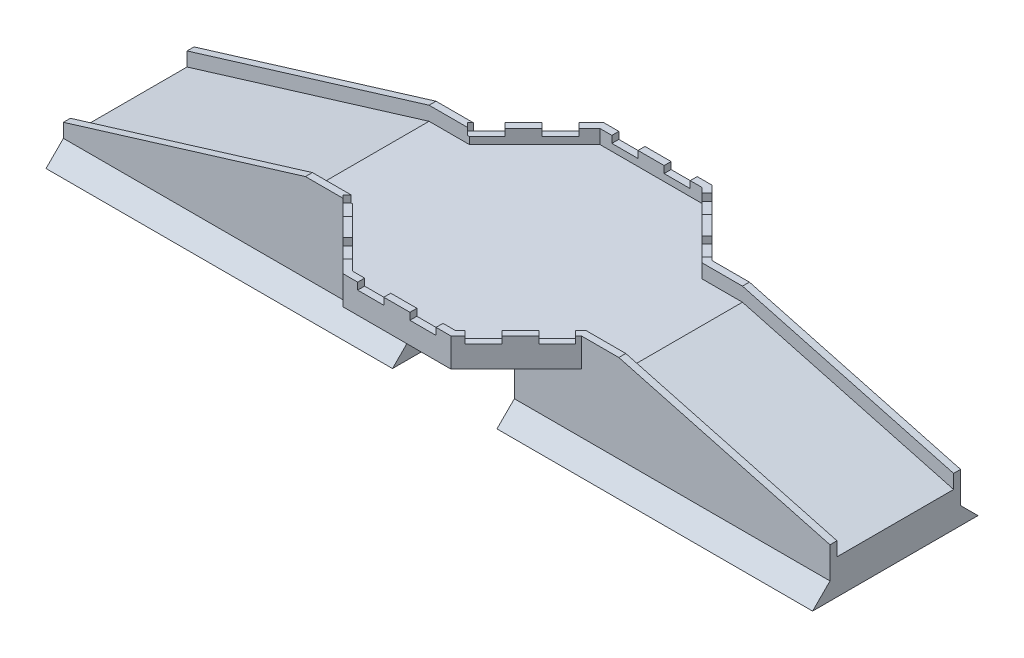
SolidWorks part; units mm, degrees
ref_plane "前视基准面" through (0, 0, 0) normal (0, 0, 1) x (1, 0, 0)
ref_plane "上视基准面" through (0, 0, 0) normal (0, 1, 0) x (1, 0, 0)
ref_plane "右视基准面" through (0, 0, 0) normal (1, 0, 0) x (0, 0, -1)
sketch "草图1" plane through (0, 0, 0) normal (0, 1, 0) x (1, 0, 0)
  line L1 (1371.3203, 750) -> (621.3203, 1500)
  line L2 (621.3203, 1500) -> (-621.3203, 1500)
  line L3 (-621.3203, 1500) -> (-1371.3203, 750)
  line L5 (-1371.3203, -750) -> (-621.3203, -1500)
  line L6 (-621.3203, -1500) -> (621.3203, -1500)
  line L7 (621.3203, -1500) -> (1371.3203, -750)
  line L9 (-1371.3203, 750) -> (-1800, 750)
  line L11 (1338.1833, 670) -> (588.1833, 1420)
  line L12 (588.1833, 1420) -> (-588.1833, 1420)
  line L13 (-588.1833, 1420) -> (-1338.1833, 670)
  line L15 (-1338.1833, -670) -> (-588.1833, -1420)
  line L16 (-588.1833, -1420) -> (588.1833, -1420)
  line L17 (588.1833, -1420) -> (1338.1833, -670)
  line L18 (-1800, 750) -> (-1800, 670)
  line L19 (-1800, 670) -> (-1338.1833, 670)
  line L20 (-1371.3203, -750) -> (-1800, -750)
  line L21 (-1800, -750) -> (-1800, -670)
  line L22 (-1800, -670) -> (-1338.1833, -670)
  line L23 (1371.3203, 750) -> (1800, 750)
  line L24 (1800, 750) -> (1800, 670)
  line L25 (1800, 670) -> (1338.1833, 670)
  line L26 (1371.3203, -750) -> (1800, -750)
  line L27 (1800, -750) -> (1800, -670)
  line L28 (1800, -670) -> (1338.1833, -670)
  line L31 (-1420, 586.3768) -> (-1420, 539.5139) [skipped]
  line L32 (-1500, 621.3203) -> (-1500, 541.3203) [skipped]
  line L33 (1420, -589.9897) -> (1420, -543.1268) [skipped]
  line L34 (1500, -621.3203) -> (1500, -541.3203) [skipped]
  dimension "D1" = 3000
  dimension "D2" = 80
  dimension "D3" = 80
  dimension "D4" = 2840
  dimension "D5" = 3600
  dimension "D6" = 3600
  dimension "D7" = 1500
  dimension "D8" = 750
  dimension "D9" = 80
  dimension "D10" = 80
  dimension "D11" = 80
  dimension "D12" = 80
  dimension "D13" = 1500
  dimension "D14" = 750
extrude "凸台-拉伸1" add sketch "草图1" along normal blind 80
sketch "草图2" plane through (0, 80, 0) normal (0, 1, 0) x (1, 0, 0)
  line L0 (588.1833, -1420) -> (-588.1833, -1420) construction
  line L1 (-150, -1420) -> (150, -1420)
  line L2 (-150, -1420) -> (-150, -1500)
  line L3 (-150, -1500) -> (150, -1500)
  line L4 (150, -1420) -> (150, -1500)
  line L5 (-621.3203, -1500) -> (621.3203, -1500) construction
  line L6 (450, -1420) -> (450, -1500)
  line L7 (450, -1500) -> (621.3203, -1500)
  line L8 (621.3203, -1500) -> (701.5537, -1419.7666)
  line L9 (621.3203, -1500) -> (1371.3203, -750) construction
  line L10 (701.5537, -1419.7666) -> (644.9852, -1363.1981)
  line L11 (1338.1833, -670) -> (588.1833, -1420) construction
  line L12 (644.9852, -1363.1981) -> (588.1833, -1420)
  line L13 (588.1833, -1420) -> (450, -1420)
  line L14 (1069.2493, -938.934) -> (857.1172, -1151.066)
  line L15 (1069.2493, -938.934) -> (1125.8178, -995.5025)
  line L16 (857.1172, -1151.066) -> (913.6858, -1207.6346)
  line L17 (1125.8178, -995.5025) -> (913.6858, -1207.6346)
  line L18 (1281.3813, -726.8019) -> (1338.1833, -670)
  line L19 (1338.1833, -670) -> (1800, -670)
  line L20 (1800, -670) -> (1800, -750)
  line L21 (1800, -750) -> (1371.3203, -750)
  line L22 (1371.3203, -750) -> (1337.9499, -783.3705)
  line L23 (1337.9499, -783.3705) -> (1281.3813, -726.8019)
  line L24 (0, 0) -> (348.169, 0)
  line L25 (-1403.7125, -717.6079) -> (-1347.1439, -661.0393)
  line L26 (-1371.3203, -750) -> (-1403.7125, -717.6079)
  line L27 (-1800, -750) -> (-1371.3203, -750)
  line L28 (-1800, -670) -> (-1800, -750)
  line L29 (-1338.1833, -670) -> (-1800, -670)
  line L30 (-1347.1439, -661.0393) -> (-1338.1833, -670)
  line L31 (-1189.2544, -932.0659) -> (-977.1224, -1144.198)
  line L32 (-920.5538, -1087.6294) -> (-977.1224, -1144.198)
  line L33 (-1132.6859, -875.4974) -> (-1189.2544, -932.0659)
  line L34 (-1132.6859, -875.4974) -> (-920.5538, -1087.6294)
  line L35 (-588.1833, -1420) -> (-450, -1420)
  line L36 (-708.4218, -1299.7615) -> (-588.1833, -1420)
  line L37 (-764.9903, -1356.33) -> (-708.4218, -1299.7615)
  line L38 (-621.3203, -1500) -> (-764.9903, -1356.33)
  line L39 (-450, -1500) -> (-621.3203, -1500)
  line L40 (-450, -1420) -> (-450, -1500)
  line L41 (-150, -1420) -> (-150, -1500)
  line L42 (150, -1420) -> (150, -1500)
  line L43 (150, 1420) -> (150, 1500)
  line L44 (-150, 1420) -> (-150, 1500)
  line L45 (-450, 1420) -> (-450, 1500)
  line L46 (-450, 1500) -> (-621.3203, 1500)
  line L47 (-621.3203, 1500) -> (-764.9903, 1356.33)
  line L48 (-764.9903, 1356.33) -> (-708.4218, 1299.7615)
  line L49 (-708.4218, 1299.7615) -> (-588.1833, 1420)
  line L50 (-588.1833, 1420) -> (-450, 1420)
  line L51 (-1132.6859, 875.4974) -> (-920.5538, 1087.6294)
  line L52 (-1132.6859, 875.4974) -> (-1189.2544, 932.0659)
  line L53 (-920.5538, 1087.6294) -> (-977.1224, 1144.198)
  line L54 (-1189.2544, 932.0659) -> (-977.1224, 1144.198)
  line L55 (-1347.1439, 661.0393) -> (-1338.1833, 670)
  line L56 (-1338.1833, 670) -> (-1800, 670)
  line L57 (-1800, 670) -> (-1800, 750)
  line L58 (-1800, 750) -> (-1371.3203, 750)
  line L59 (-1371.3203, 750) -> (-1403.7125, 717.6079)
  line L60 (-1403.7125, 717.6079) -> (-1347.1439, 661.0393)
  line L61 (1337.9499, 783.3705) -> (1281.3813, 726.8019)
  line L62 (1337.9499, 783.3705) -> (1371.3203, 750)
  line L63 (1371.3203, 750) -> (1800, 750)
  line L64 (1800, 750) -> (1800, 670)
  line L65 (1800, 670) -> (1338.1833, 670)
  line L66 (1338.1833, 670) -> (1281.3813, 726.8019)
  line L67 (1125.8178, 995.5025) -> (913.6858, 1207.6346)
  line L68 (857.1172, 1151.066) -> (913.6858, 1207.6346)
  line L69 (1069.2493, 938.934) -> (1125.8178, 995.5025)
  line L70 (1069.2493, 938.934) -> (857.1172, 1151.066)
  line L71 (588.1833, 1420) -> (450, 1420)
  line L72 (644.9852, 1363.1981) -> (588.1833, 1420)
  line L73 (701.5537, 1419.7666) -> (644.9852, 1363.1981)
  line L74 (621.3203, 1500) -> (701.5537, 1419.7666)
  line L75 (450, 1500) -> (621.3203, 1500)
  line L76 (450, 1420) -> (450, 1500)
  line L77 (150, 1420) -> (150, 1500)
  line L78 (-150, 1500) -> (150, 1500)
  line L79 (-150, 1420) -> (-150, 1500)
  line L80 (-150, 1420) -> (150, 1420)
  line L82 (-1800, -670) -> (-1800, -750) construction
  line L83 (-1338.1833, -670) -> (-1800, -670) construction
  line L84 (-1800, -750) -> (-1371.3203, -750) construction
  line L85 (-1371.3203, -750) -> (-621.3203, -1500) construction
  line L86 (-588.1833, -1420) -> (-1338.1833, -670) construction
  point P11 (150, -1460)
  point P22 (963.1833, -1045)
  dimension "D1" = 300
  dimension "D2" = 150
  dimension "D3" = 300
  dimension "D4" = 300
  dimension "D5" = 150
  dimension "D6" = 300
  dimension "D7" = 300
  dimension "D8" = 0
  dimension "D9" = 0
  dimension "D10" = 0
  dimension "D11" = 0
  dimension "D12" = 0
extrude "凸台-拉伸2" add sketch "草图2" along normal blind 80
sketch "草图3" plane through (0, 0, 0) normal (0, -1, 0) x (1, 0, 0)
  line L0 (-1800, 750) -> (-1800, -750)
  line L1 (-1800, -750) -> (-1371.3203, -750)
  line L2 (-1371.3203, -750) -> (-621.3203, -1500)
  line L3 (-621.3203, -1500) -> (621.3203, -1500)
  line L4 (621.3203, -1500) -> (1371.3203, -750)
  line L5 (1371.3203, -750) -> (1800, -750)
  line L6 (1800, -750) -> (1800, 750)
  line L7 (1800, 750) -> (1371.3203, 750)
  line L8 (1371.3203, 750) -> (621.3203, 1500)
  line L9 (621.3203, 1500) -> (-621.3203, 1500)
  line L10 (-621.3203, 1500) -> (-1371.3203, 750)
  line L11 (-1371.3203, 750) -> (-1800, 750)
extrude "凸台-拉伸3" add sketch "草图3" along normal blind 170
sketch "草图4" plane through (0, 0, 750) normal (0, 0, 1) x (1, 0, 0)
  line L0 (-600, 0) -> (-1800, 0)
  line L1 (-1800, -170) -> (-1800, 160) construction
  line L2 (-4580.2247, -1050) -> (-4580.2247, -850)
  line L3 (-4580.2247, -1050) -> (-600, -1050)
  line L4 (-600, -1050) -> (-600, 0)
  line L5 (-1800, 160) -> (-1371.3203, 160) construction
  line L6 (-4580.2247, -850) -> (-1800, 0)
  line L7 (600, 0) -> (1800, 0)
  line L8 (1800, 0) -> (4225.833, -650)
  line L9 (4225.833, -650) -> (4225.833, -1050)
  line L10 (4225.833, -1050) -> (600, -1050)
  line L11 (600, -1050) -> (600, 0)
  dimension "D1" = 1210
  dimension "D2" = 600
  dimension "D3" = 160
  dimension "D4" = 17
  dimension "D5" = 200
  dimension "D6" = 600
  dimension "D7" = 400
  dimension "D8" = 15
extrude "凸台-拉伸4" add sketch "草图4" against normal up to surface (1500 mm away) up to face at (-1542.7922, 12, -750)
sketch "草图5" plane through (0, 0, -750) normal (0, 0, -1) x (-1, 0, 0)
  line L0 (-4225.833, -650) -> (-1800, 0)
  line L1 (-1800, 0) -> (-1800, 160)
  line L2 (-1800, 160) -> (-4225.833, -490)
  line L3 (-4225.833, -490) -> (-4225.833, -650)
  line L4 (4580.2247, -850) -> (1800, 0)
  line L5 (1800, 0) -> (1800, 160)
  line L6 (1800, 160) -> (4580.2247, -690)
  line L7 (4580.2247, -690) -> (4580.2247, -850)
extrude "凸台-拉伸5" add sketch "草图5" against normal blind 80
mirror "镜向1" about plane through (0, 0, 0) normal (0, 0, 1) of "凸台-拉伸5"
sketch "草图6" plane through (-600, 0, 0) normal (1, 0, 0) x (0, 0, -1)
  line L0 (750, -850) -> (950, -1050)
  line L1 (750, -170) -> (750, -1050) construction
  line L2 (950, -1050) -> (-950, -1050)
  line L3 (-950, -1050) -> (-750, -850)
  line L4 (-750, -1050) -> (-750, -170) construction
  line L5 (-750, -850) -> (750, -850)
  dimension "D1" = 200
  dimension "D2" = 45
  dimension "D3" = 45
extrude "凸台-拉伸6" add sketch "草图6" against normal up to surface and the other way up to surface
sketch "草图7" plane through (0, 0, 750) normal (0, 0, 1) x (1, 0, 0)
  line L0 (-4580.2247, -1050) -> (4225.833, -1050) construction
  line L1 (-600, -850) -> (600, -850)
  line L2 (-600, -850) -> (-600, -1050)
  line L3 (-600, -1050) -> (600, -1050)
  line L4 (600, -850) -> (600, -1050)
extrude "切除-拉伸1" cut sketch "草图7" against normal through all and the other way through all
